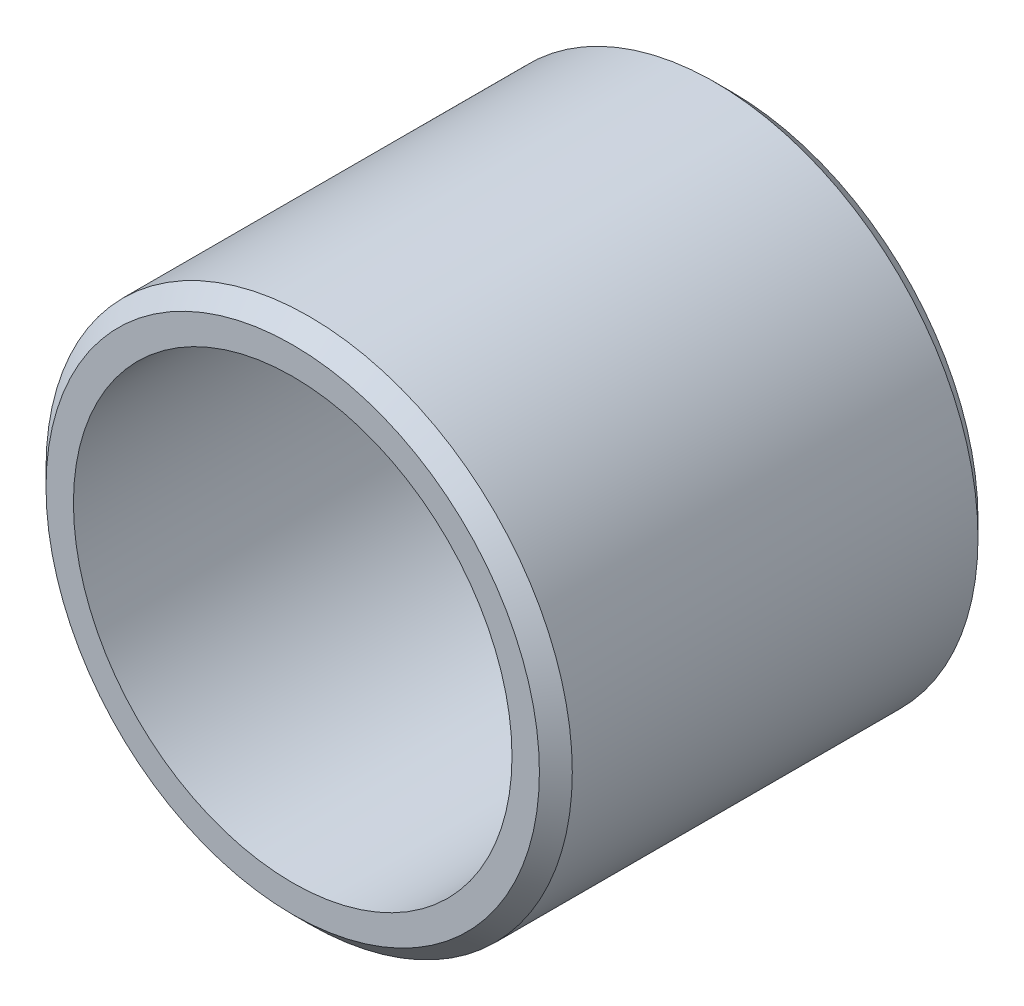
SolidWorks part; units mm, degrees
ref_plane "Front Plane" through (0, 0, 0) normal (0, 0, 1) x (1, 0, 0)
ref_plane "Top Plane" through (0, 0, 0) normal (0, 1, 0) x (1, 0, 0)
ref_plane "Right Plane" through (0, 0, 0) normal (1, 0, 0) x (0, 0, -1)
sketch "Sketch1" plane through (0, 0, 0) normal (1, 0, 0) x (0, 0, -1)
  line L0 (-25, 0) -> (25, 0) construction
  line L1 (25, 30) -> (25, -30) construction
  line L2 (-25, 30) -> (-25, -30) construction
  line L3 (25, 30) -> (-25, 30) construction
  line L4 (25, -30) -> (-25, -30) construction
  line L5 (-25, 25) -> (25, 25) construction
  line L6 (-25, -25) -> (25, -25) construction
  point P2 (0, 0)
  point P7 (-25, 0)
  point P8 (-25, -25)
  point P9 (25, 0)
  point P11 (-25, 25)
  dimension "OD" = 60
  dimension "ID" = 50
  dimension "Length" = 50
sketch "Sketch2" plane through (0, 0, 0) normal (0, 0, 1) x (1, 0, 0)
  line L0 (-30, 0) -> (30, 0) construction
  line L1 (0, -30) -> (0, 30) construction
  circle A0 centre (0, 0) radius 25 construction
  circle A1 centre (0, 0) radius 30 construction
  point P16 (0, 0)
  dimension "ID" = 50
  dimension "OD" = 60
sketch "Sketch3" plane through (0, 0, 0) normal (1, 0, 0) x (0, 0, -1)
  line L0 (-25, 25) -> (25, 25)
  line L1 (25, 30) -> (25, -30) construction
  line L2 (25, 25) -> (25, 30)
  line L5 (25, 30) -> (-25, 30)
  line L6 (-25, 30) -> (-25, 25)
  line L7 (-25, 0) -> (25, 0) construction
revolve "Revolve1" add sketch "Sketch3" angle 360 about L7
chamfer "Chamfer1" distance 1.875 angle 45 2 edges at (30, 0, 25) (30, 0, -25)
equation "\"D1@Chamfer1\"=((\"OD@Sketch1\"-\"ID@Sketch1\")/2)*.375"
